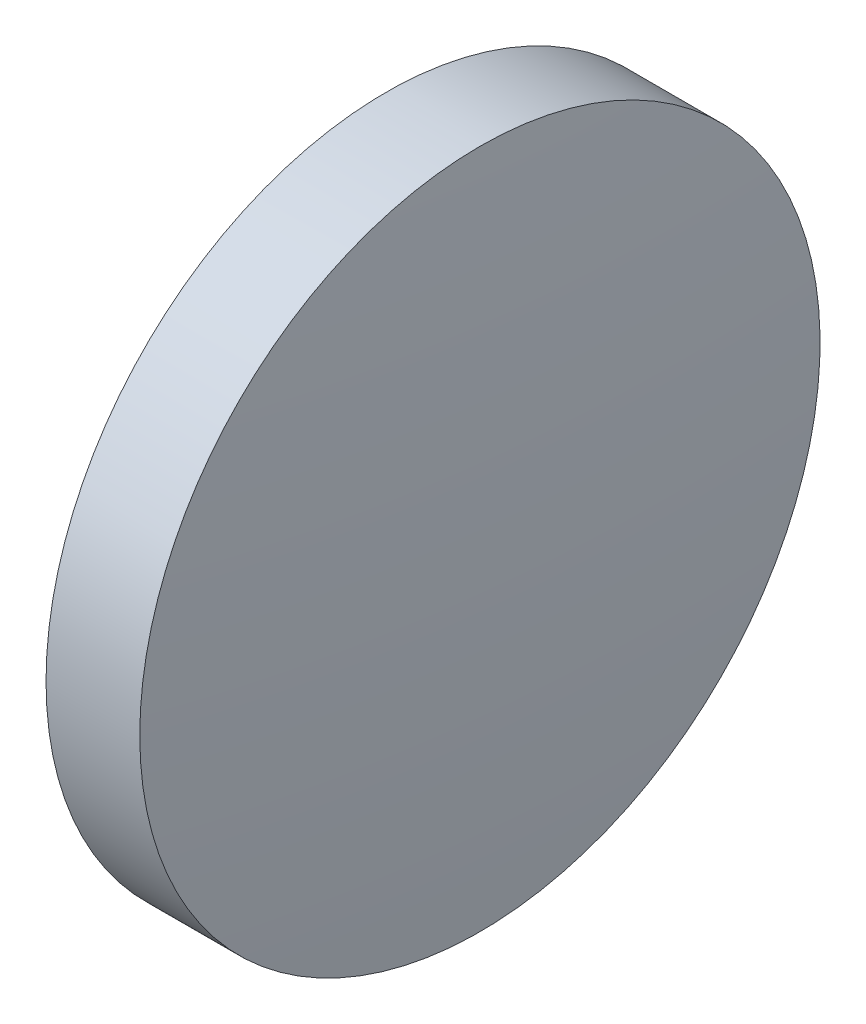
SolidWorks part; units mm, degrees
ref_plane "前视基准面" through (0, 0, 0) normal (0, 0, 1) x (1, 0, 0)
ref_plane "上视基准面" through (0, 0, 0) normal (0, 1, 0) x (1, 0, 0)
ref_plane "右视基准面" through (0, 0, 0) normal (1, 0, 0) x (0, 0, -1)
sketch "草图1" plane through (0, 0, 0) normal (0, 0, 1) x (1, 0, 0)
  line L0 (110.1654, 65.2336) -> (128.9614, 65.2336) construction
  line L1 (115.7646, 65.2336) -> (115.7646, 77.9336)
  line L2 (119.7646, 65.2336) -> (115.7646, 65.2336)
  line L5 (115.7646, 77.9336) -> (119.2646, 77.9336)
  arc A0 (119.7646, 65.2336) -> (119.2646, 77.9336) centre (-41.7754, 65.2336) ccw
revolve "旋转1" add sketch "草图1" angle 360 about L0
